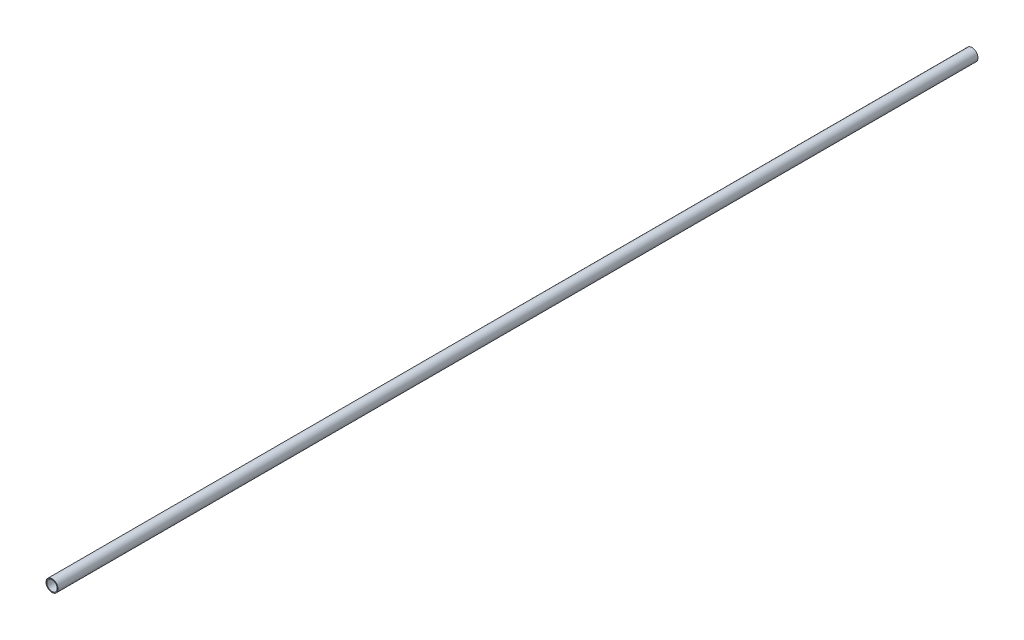
SolidWorks part; units mm, degrees
ref_plane "Front Plane" through (0, 0, 0) normal (0, 0, 1) x (1, 0, 0)
ref_plane "Top Plane" through (0, 0, 0) normal (0, 1, 0) x (1, 0, 0)
ref_plane "Right Plane" through (0, 0, 0) normal (1, 0, 0) x (0, 0, -1)
sketch "Sketch1" plane through (0, 0, 0) normal (0, 0, 1) x (1, 0, 0)
  circle A0 centre (0, 0) radius 5.5
  dimension "D1" = 11
extrude "Extrude-Thin1" add sketch "Sketch1" along normal blind 976 thin
